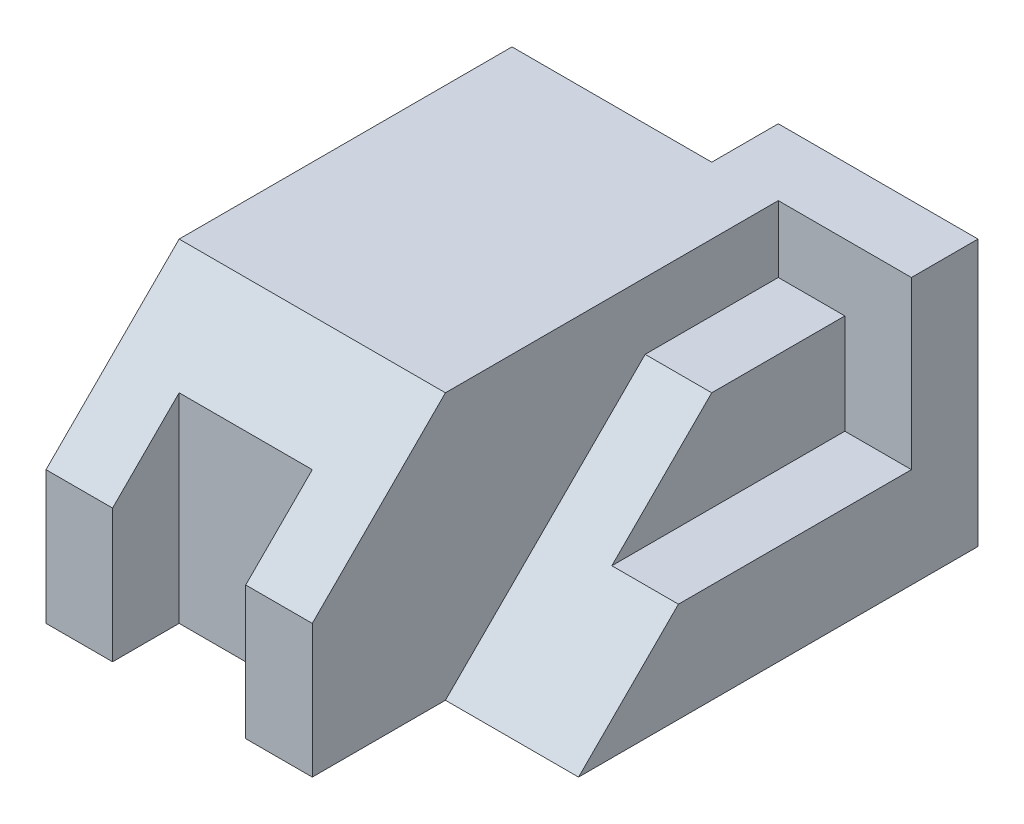
SolidWorks part; units mm, degrees
ref_plane "Front Plane" through (0, 0, 0) normal (0, 0, 1) x (1, 0, 0)
ref_plane "Top Plane" through (0, 0, 0) normal (0, 1, 0) x (1, 0, 0)
ref_plane "Right Plane" through (0, 0, 0) normal (1, 0, 0) x (0, 0, -1)
sketch "Sketch1" plane through (0, 0, 0) normal (0, 1, 0) x (1, 0, 0)
  line L0 (0, 0) -> (30, 0)
  line L1 (30, 0) -> (30, 10)
  line L2 (30, 10) -> (60, 10)
  line L3 (60, 10) -> (60, -60)
  line L4 (60, -60) -> (40, -60)
  line L5 (40, -60) -> (40, -70)
  line L6 (40, -70) -> (30, -70)
  line L7 (30, -70) -> (30, -60)
  line L8 (30, -60) -> (10, -60)
  line L9 (10, -60) -> (10, -70)
  line L10 (10, -70) -> (0, -70)
  line L11 (0, -70) -> (0, 0)
  dimension "D1" = 70
  dimension "D2" = 30
  dimension "D3" = 30
  dimension "D4" = 70
  dimension "D5" = 20
  dimension "D6" = 10
  dimension "D7" = 10
  dimension "D8" = 10
  dimension "D9" = 10
  dimension "D10" = 10
extrude "Boss-Extrude1" add sketch "Sketch1" along normal blind 40
chamfer "Chamfer1" distance 20 1 edges at (5, 40, 70)
sketch "Sketch2" plane through (60, 0, 0) normal (1, 0, 0) x (0, 0, -1)
  line L0 (-60, 0) -> (10, 0) construction
  line L1 (0, 30) -> (0, 40)
  line L2 (-50, 0) -> (-20, 30)
  line L3 (-20, 30) -> (0, 30)
  line L4 (-50, 0) -> (-60, 0)
  line L5 (-60, 0) -> (-60, 30)
  line L6 (-60, 30) -> (-50, 40)
  line L7 (0, 40) -> (-50, 40)
  line L8 (-50, 40) -> (10, 40) construction
  point P0 (-50, 0)
  point P1 (-20, 30)
  point P4 (0, 30)
  point P5 (0, 0)
  dimension "D1" = 30
  dimension "D2" = 10
  dimension "D3" = 30
extrude "Cut-Extrude1" cut sketch "Sketch2" against normal blind 20
sketch "Sketch3" plane through (0, 0, 70) normal (0, 0, 1) x (1, 0, 0)
  line L0 (60, 15) -> (50, 15)
  line L1 (60, 0) -> (60, 30) construction
  line L2 (50, 15) -> (50, 30)
  line L3 (50, 30) -> (60, 30)
  line L4 (60, 30) -> (60, 15)
  dimension "D1" = 15
  dimension "D2" = 10
extrude "Cut-Extrude2" cut sketch "Sketch3" against normal blind 70
